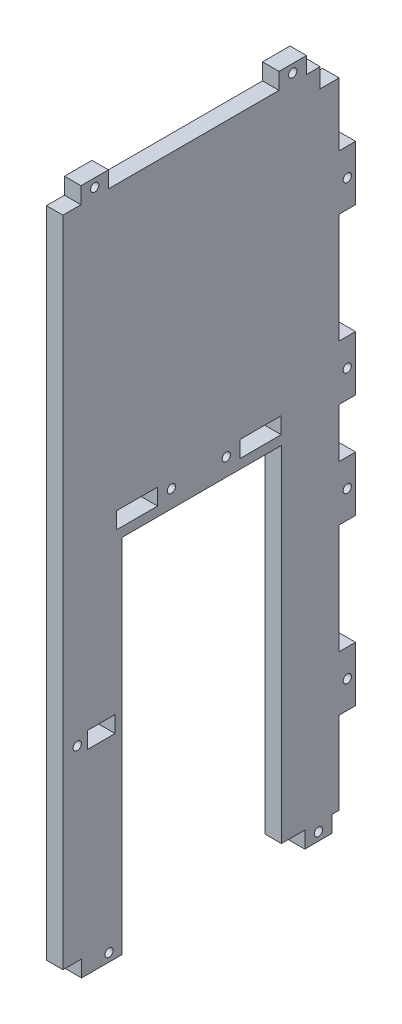
SolidWorks part; units mm, degrees
ref_plane "Plan de face" through (0, 0, 0) normal (0, 0, 1) x (1, 0, 0)
ref_plane "Plan de dessus" through (0, 0, 0) normal (0, 1, 0) x (1, 0, 0)
ref_plane "Plan de droite" through (0, 0, 0) normal (1, 0, 0) x (0, 0, -1)
sketch "Esquisse1" plane through (0, 0, 0) normal (1, 0, 0) x (0, 0, -1)
  line L0 (97.1531, 0) -> (-102.2664, 0) construction
  line L1 (-50.29, 119) -> (50.29, 119)
  line L2 (-50.29, 119) -> (-50.29, -119)
  line L3 (-50.29, -119) -> (50.29, -119)
  line L4 (50.29, 119) -> (50.29, -119)
  line L5 (0, 172.7153) -> (0, -236.1933) construction
  line L7 (-41.29, -48) -> (-31.29, -48)
  line L8 (-41.29, -48) -> (-41.29, -54)
  line L9 (-41.29, -54) -> (-31.29, -54)
  line L10 (-31.29, -48) -> (-31.29, -54)
  line L15 (-30.795, 16) -> (-15.795, 16)
  line L16 (-30.795, 16) -> (-30.795, 10)
  line L17 (-30.795, 10) -> (-15.795, 10)
  line L18 (-15.795, 16) -> (-15.795, 10)
  line L19 (14.205, 16) -> (29.205, 16)
  line L20 (14.205, 16) -> (14.205, 10)
  line L21 (14.205, 10) -> (29.205, 10)
  line L22 (29.205, 16) -> (29.205, 10)
  dimension "D1" = 238
  dimension "D2" = 100.58
  dimension "D4" = 119
  dimension "D13" = 15
  dimension "D14" = 15
  dimension "D15" = 30
  dimension "D16" = 6
  dimension "D17" = 6
  dimension "D3" = 50.29
  dimension "D6" = 19.495
  dimension "D7" = 9
  dimension "D8" = 167
  dimension "D9" = 6
  dimension "D10" = 10
  dimension "D5" = 103
extrude "Boss.-Extru.1" add sketch "Esquisse1" along normal blind 6
sketch "Esquisse3" plane through (6, 0, 0) normal (1, 0, 0) x (0, 0, -1)
  line L0 (-50.29, -119) -> (50.29, -119) construction
  line L1 (-43.5, -119) -> (-23.5, -119)
  line L2 (-43.5, -119) -> (-43.5, -125)
  line L3 (-43.5, -125) -> (-23.5, -125)
  line L4 (-23.5, -119) -> (-23.5, -125)
  line L5 (245.3741, 0) -> (-166.5298, 0) construction
  line L6 (50.29, -119) -> (50.29, 119) construction
  line L7 (37.79, -119) -> (47.79, -119)
  line L8 (37.79, -119) -> (37.79, -125)
  line L9 (37.79, -125) -> (47.79, -125)
  line L10 (0, 208.6671) -> (0, -232.3841) construction
  line L12 (47.79, -119) -> (47.79, -125)
  line L13 (56.29, 29) -> (56.29, 9)
  line L14 (50.29, 9) -> (56.29, 9)
  line L15 (50.29, 29) -> (50.29, 9)
  line L16 (50.29, 29) -> (56.29, 29)
  line L17 (56.29, 89) -> (56.29, 69)
  line L18 (50.29, 69) -> (56.29, 69)
  line L19 (50.29, 89) -> (50.29, 69)
  line L20 (50.29, 89) -> (56.29, 89)
  line L21 (50.29, 119) -> (-50.29, 119) construction
  line L22 (50.29, -89) -> (56.29, -89)
  line L23 (50.29, -89) -> (50.29, -69)
  line L24 (50.29, -69) -> (56.29, -69)
  line L25 (56.29, -89) -> (56.29, -69)
  line L26 (50.29, -29) -> (56.29, -29)
  line L27 (50.29, -29) -> (50.29, -9)
  line L28 (50.29, -9) -> (56.29, -9)
  line L29 (0, -208.6671) -> (0, 232.3841) construction
  line L30 (-50.29, 119) -> (-50.29, -119) construction
  line L34 (50.29, -119) -> (50.29, 119) construction
  line L35 (56.29, -29) -> (56.29, -9)
  line L36 (38.41, 119) -> (28.41, 119)
  line L37 (38.41, 119) -> (38.41, 125)
  line L38 (38.41, 125) -> (28.41, 125)
  line L39 (28.41, 119) -> (28.41, 125)
  line L40 (-50.29, 119) -> (-50.29, -119) construction
  line L41 (-33.71, 119) -> (-43.71, 119)
  line L42 (-33.71, 119) -> (-33.71, 125)
  line L43 (-33.71, 125) -> (-43.71, 125)
  line L44 (-43.71, 119) -> (-43.71, 125)
  dimension "D2" = 20
  dimension "D3" = 6
  dimension "D4" = 10
  dimension "D5" = 6.79
  dimension "D6" = 6
  dimension "D7" = 6
  dimension "D8" = 20
  dimension "D9" = 6
  dimension "D10" = 20
  dimension "D11" = 2.5
  dimension "D14" = 30
  dimension "D15" = 40
  dimension "D16" = 6
  dimension "D17" = 10
  dimension "D18" = 11.88
  dimension "D19" = 6.58
  dimension "D20" = 10
  dimension "D21" = 6
extrude "Boss.-Extru.5" add sketch "Esquisse3" against normal blind 6
sketch "Esquisse6" plane through (6, 0, 0) normal (1, 0, 0) x (0, 0, -1)
  line L1 (-28.71, -125) -> (29.29, -125)
  line L2 (-28.71, -125) -> (-28.71, 6.59)
  line L3 (-28.71, 6.59) -> (29.29, 6.59)
  line L4 (29.29, -125) -> (29.29, 6.59)
  line L5 (50.29, -69) -> (50.29, -29) construction
  line L8 (28.41, 119) -> (-33.71, 119) construction
  dimension "D1" = 58
  dimension "D2" = 112.41
  dimension "D3" = 21
extrude "Enlèv. mat.-Extru.2" cut sketch "Esquisse6" against normal blind 6
sketch "Esquisse7" plane through (0, 0, 0) normal (-1, 0, 0) x (0, 0, 1)
  line L1 (-50.29, 119) -> (-43.41, 119)
  line L2 (-50.29, 119) -> (-50.29, 112)
  line L3 (-50.29, 112) -> (-43.41, 112)
  line L4 (-43.41, 119) -> (-43.41, 112)
  dimension "D1" = 7
  dimension "D2" = 6.88
extrude "Enlèv. mat.-Extru.3" cut sketch "Esquisse7" against normal blind 6
sketch "Esquisse8" plane through (0, 0, 0) normal (-1, 0, 0) x (0, 0, 1)
  line L0 (-51.0214, 13) -> (44.3386, 13) construction
  line L1 (43.5, -125) -> (28.71, -125) construction
  line L2 (28.71, 6.59) -> (28.71, -125) construction
  line L4 (30.795, 10) -> (15.795, 10) construction
  line L5 (60.5401, -51) -> (10.4957, -51) construction
  line L6 (41.29, -48) -> (41.29, -54) construction
  line L8 (41.29, -54) -> (31.29, -54) construction
  line L9 (53.2872, 122) -> (-67.0711, 122) construction
  line L10 (33.71, 125) -> (43.71, 125) construction
  line L11 (-28.41, 125) -> (-28.41, 119) construction
  line L12 (33.71, 119) -> (33.71, 125) construction
  line L13 (-67.0711, -122) -> (72.8873, -122) construction
  line L14 (15.795, 10) -> (15.795, 16) construction
  line L15 (-14.205, 16) -> (-14.205, 10) construction
  line L16 (-37.79, -119) -> (-37.79, -125) construction
  line L18 (-53.29, 135.0788) -> (-53.29, -173.0788) construction
  line L19 (-56.29, 69) -> (-56.29, 89) construction
  line L21 (-56.29, -69) -> (-50.29, -69) construction
  line L22 (-50.29, 9) -> (-56.29, 9) construction
  line L23 (-56.29, 89) -> (-50.29, 89) construction
  circle A1 centre (-9.205, 13) radius 1.5
  circle A2 centre (10.795, 13) radius 1.5
  circle A5 centre (45.08, -51) radius 1.5
  circle A6 centre (38.71, 122) radius 1.5
  circle A7 centre (-33.41, 122) radius 1.5
  circle A8 centre (33.5, -122) radius 1.5
  circle A9 centre (-53.29, 79) radius 1.5
  circle A10 centre (-42.79, -122) radius 1.5
  circle A11 centre (-53.29, 19) radius 1.5
  circle A12 centre (-53.29, -79) radius 1.5
  circle A13 centre (-53.29, -19) radius 1.5
  point P8 (23.295, 10)
  dimension "D1" = 3
  dimension "D2" = 3
  dimension "D4" = 3
  dimension "D5" = 3
  dimension "D6" = 5
  dimension "D7" = 5
  dimension "D8" = 4.79
  dimension "D10" = 3
  dimension "D15" = 3
  dimension "D16" = 3
  dimension "D17" = 5
  dimension "D18" = 5
  dimension "D20" = 3
  dimension "D21" = 3
  dimension "D22" = 3
  dimension "D23" = 3
  dimension "D24" = 5
  dimension "D26" = 3
  dimension "D27" = 3
  dimension "D28" = 3
  dimension "D29" = 10
  dimension "D31" = 10
  dimension "D32" = 10
  dimension "D11" = 3.79
  dimension "D13" = 3
  dimension "D14" = 3
  dimension "D30" = 10
extrude "Enlèv. mat.-Extru.4" cut sketch "Esquisse8" against normal blind 6
equation "\"D3@Esquisse1\"=\"D2@Esquisse1\"/2"
equation "\"D4@Esquisse1\"=\"D1@Esquisse1\"/2"
